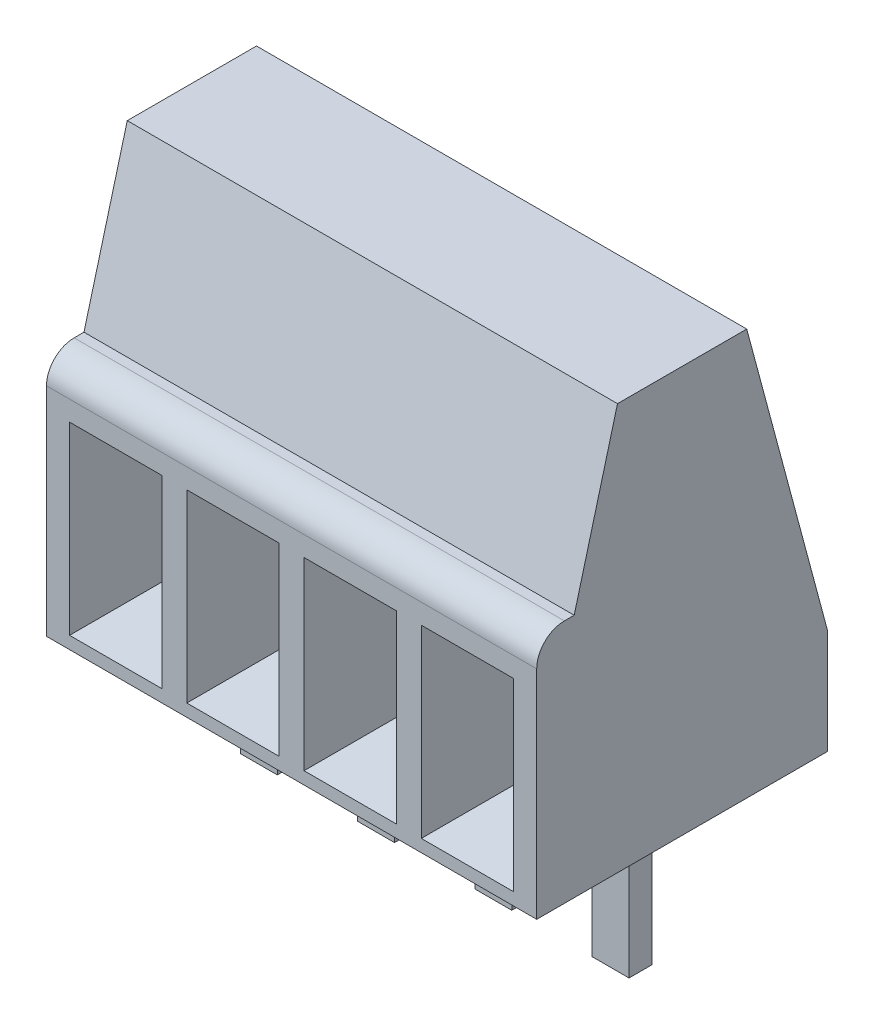
SolidWorks part; units mm, degrees
ref_plane "Front Plane" through (0, 0, 0) normal (0, 0, 1) x (1, 0, 0)
ref_plane "Top Plane" through (0, 0, 0) normal (0, 1, 0) x (1, 0, 0)
ref_plane "Right Plane" through (0, 0, 0) normal (1, 0, 0) x (0, 0, -1)
sketch "Sketch1" plane through (0, 0, 0) normal (0, 1, 0) x (1, 0, 0)
  line L1 (-5.31, -3.15) -> (5.31, -3.15)
  line L2 (-5.31, -3.15) -> (-5.31, 3.15)
  line L3 (-5.31, 3.15) -> (5.31, 3.15)
  line L4 (5.31, -3.15) -> (5.31, 3.15)
  line L5 (-5.31, -3.15) -> (5.31, 3.15) construction
  line L6 (-5.31, 3.15) -> (5.31, -3.15) construction
  point P0 (0, 0)
  dimension "D1" = 10.62
  dimension "D2" = 6.3
extrude "Boss-Extrude1" add sketch "Sketch1" along normal blind 8.8
sketch "Sketch2" plane through (0, 0, 0) normal (0, 1, 0) x (1, 0, 0)
  line L0 (5.31, 3.15) -> (-5.31, 3.15) construction
  line L1 (0.87, -0.05) -> (1.67, -0.05)
  line L2 (0.87, -0.05) -> (0.87, 0.45)
  line L3 (0.87, 0.45) -> (1.67, 0.45)
  line L4 (1.67, -0.05) -> (1.67, 0.45)
  line L5 (0.87, -0.05) -> (1.67, 0.45) construction
  line L6 (0.87, 0.45) -> (1.67, -0.05) construction
  line L7 (3.41, -0.05) -> (4.21, -0.05)
  line L8 (3.41, -0.05) -> (3.41, 0.45)
  line L9 (3.41, 0.45) -> (4.21, 0.45)
  line L10 (4.21, -0.05) -> (4.21, 0.45)
  line L11 (3.41, -0.05) -> (4.21, 0.45) construction
  line L12 (3.41, 0.45) -> (4.21, -0.05) construction
  line L13 (-0.87, -0.05) -> (-1.67, -0.05)
  line L14 (-0.87, -0.05) -> (-0.87, 0.45)
  line L15 (-0.87, 0.45) -> (-1.67, 0.45)
  line L16 (-1.67, -0.05) -> (-1.67, 0.45)
  line L17 (-0.87, -0.05) -> (-1.67, 0.45) construction
  line L18 (-0.87, 0.45) -> (-1.67, -0.05) construction
  line L19 (-3.41, -0.05) -> (-4.21, -0.05)
  line L20 (-3.41, -0.05) -> (-3.41, 0.45)
  line L21 (-3.41, 0.45) -> (-4.21, 0.45)
  line L22 (-4.21, -0.05) -> (-4.21, 0.45)
  line L23 (-3.41, -0.05) -> (-4.21, 0.45) construction
  line L24 (-3.41, 0.45) -> (-4.21, -0.05) construction
  point P0 (1.27, 0.2)
  point P6 (3.81, 0.2)
  point P11 (-1.27, 0.2)
  point P20 (1.27, 0.2)
  point P22 (-3.81, 0.2)
  dimension "D1" = 2.54
  dimension "D2" = 2.54
  dimension "D3" = 0.8
  dimension "D4" = 2.54
  dimension "D5" = 1.27
  dimension "D6" = 0.5
  dimension "D7" = 2.95
extrude "Boss-Extrude2" add sketch "Sketch2" against normal blind 3.2
sketch "Sketch3" plane through (5.31, 0, 0) normal (1, 0, 0) x (0, 0, -1)
  line L1 (-3.15, 8.8) -> (-3.15, 0) construction
  line L2 (-2.55, 5.3) -> (-2.3378, 5.3)
  line L3 (-2.3378, 5.3) -> (-1.4, 8.8)
  line L4 (-3.15, 8.8) -> (3.15, 8.8) construction
  line L5 (-1.4, 8.8) -> (1.4, 8.8)
  line L6 (1.4, 8.8) -> (3.15, 2.2689)
  line L7 (3.15, 8.8) -> (3.15, 0) construction
  line L10 (1.4, 8.8) -> (3.15, 8.8)
  line L11 (3.15, 8.8) -> (3.15, 2.2689)
  line L12 (-3.15, 4.7) -> (-3.15, 8.8)
  line L13 (-3.15, 8.8) -> (-1.4, 8.8)
  line L14 (-3.15, 0) -> (3.15, 0) construction
  arc A0 (-3.15, 4.7) -> (-2.55, 5.3) centre (-2.55, 4.7) cw
  point P18 (0, 8.8)
  line M12 (3.15, 0) -> (3.15, 8.8)
  line M13 (3.15, 8.8) -> (-3.15, 8.8)
  line M14 (-3.15, 8.8) -> (-3.15, 0)
  dimension "D3" = 4.7
  dimension "D1" = 15
  dimension "D2" = 75
  dimension "D4" = 2.8
  dimension "D5" = 5.3
extrude "Cut-Extrude1" cut sketch "Sketch3" against normal up to next contours A0 L2 L3 M14 M13 | L6 M13 M12
sketch "Sketch4" plane through (0, 0, 3.15) normal (0, 0, 1) x (1, 0, 0)
  line L1 (-4.81, 0.2689) -> (-2.81, 0.2689)
  line L2 (-4.81, 0.2689) -> (-4.81, 4.2689)
  line L3 (-4.81, 4.2689) -> (-2.81, 4.2689)
  line L4 (-2.81, 0.2689) -> (-2.81, 4.2689)
  line L5 (-4.81, 0.2689) -> (-2.81, 4.2689) construction
  line L6 (-4.81, 4.2689) -> (-2.81, 0.2689) construction
  line L7 (-2.27, 0.2689) -> (-0.27, 0.2689)
  line L8 (-2.27, 0.2689) -> (-2.27, 4.2689)
  line L9 (-2.27, 4.2689) -> (-0.27, 4.2689)
  line L10 (-0.27, 0.2689) -> (-0.27, 4.2689)
  line L11 (-2.27, 0.2689) -> (-0.27, 4.2689) construction
  line L12 (-2.27, 4.2689) -> (-0.27, 0.2689) construction
  line L13 (2.27, 4.2689) -> (0.27, 4.2689)
  line L14 (2.27, 4.2689) -> (2.27, 0.2689)
  line L15 (2.27, 0.2689) -> (0.27, 0.2689)
  line L16 (0.27, 4.2689) -> (0.27, 0.2689)
  line L17 (2.27, 4.2689) -> (0.27, 0.2689) construction
  line L18 (2.27, 0.2689) -> (0.27, 4.2689) construction
  line L20 (4.81, 4.2689) -> (2.81, 4.2689)
  line L21 (4.81, 4.2689) -> (4.81, 0.2689)
  line L22 (4.81, 0.2689) -> (2.81, 0.2689)
  line L23 (2.81, 4.2689) -> (2.81, 0.2689)
  line L25 (2.81, 4.2689) -> (4.81, 0.2689) construction
  line L26 (-4.21, -3.2) -> (-3.41, -3.2) construction
  line L27 (2.81, 0.2689) -> (4.81, 4.2689) construction
  line L28 (3.41, -3.2) -> (4.21, -3.2) construction
  line L29 (0.87, -3.2) -> (1.67, -3.2) construction
  line L30 (-1.67, -3.2) -> (-0.87, -3.2) construction
  point P0 (-3.81, 2.2689)
  point P5 (-1.27, 2.2689)
  point P10 (1.27, 2.2689)
  point P21 (0, 2.2689)
  point P23 (3.81, -3.2)
  point P24 (3.81, 2.2689)
  point P31 (-3.81, -3.2)
  point P32 (1.27, -3.2)
  point P35 (-1.27, -3.2)
  dimension "D1" = 2
  dimension "D2" = 4
extrude "Cut-Extrude2" cut sketch "Sketch4" against normal blind 3.15 draft 10
